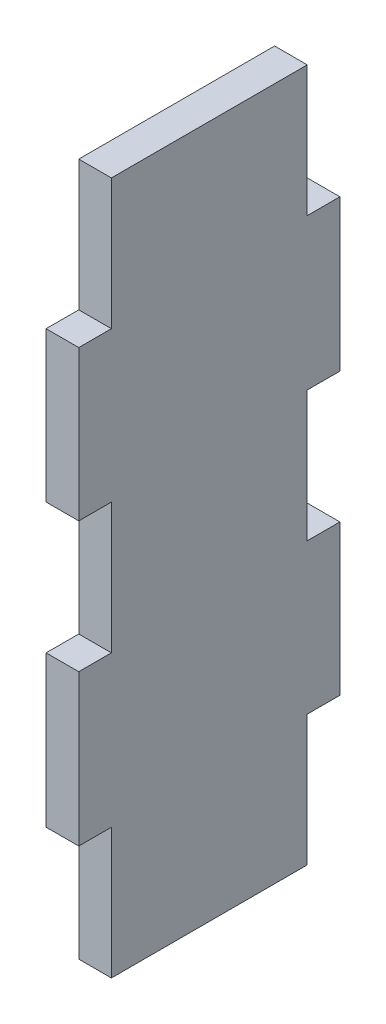
SolidWorks part; units mm, degrees
ref_plane "Front Plane" through (0, 0, 0) normal (0, 0, 1) x (1, 0, 0)
ref_plane "Top Plane" through (0, 0, 0) normal (0, 1, 0) x (1, 0, 0)
ref_plane "Right Plane" through (0, 0, 0) normal (1, 0, 0) x (0, 0, -1)
sketch "Sketch1" plane through (0, 0, 0) normal (0, 0, 1) x (1, 0, 0)
  line L0 (451.1075, 187.1755) -> (451.1075, 119.7813)
  line L1 (451.1075, 119.7813) -> (454.2825, 119.7813)
  line L2 (454.2825, 119.7813) -> (454.2825, 187.1755)
  line L3 (454.2825, 187.1755) -> (451.1075, 187.1755)
  dimension "D1" = 3.175
extrude "Boss-Extrude1" add sketch "Sketch1" against normal up to surface (25.4 mm away) contours L2 L3 L0 L1
sketch "Sketch2" plane through (454.2825, 0, 0) normal (1, 0, 0) x (0, 0, -1)
  line L0 (3.175, 84.4459) -> (3.175, 234.4049) construction
  line L1 (0, 187.1755) -> (3.175, 187.1755)
  line L2 (0, 187.1755) -> (0, 174.4755)
  line L3 (0, 174.4755) -> (3.175, 174.4755)
  line L4 (3.175, 187.1755) -> (3.175, 174.4755)
  line L5 (22.225, 234.4049) -> (22.225, 84.4459) construction
  line L6 (22.225, 174.4755) -> (25.4, 174.4755)
  line L7 (22.225, 174.4755) -> (22.225, 187.1755)
  line L8 (22.225, 187.1755) -> (25.4, 187.1755)
  line L9 (25.4, 174.4755) -> (25.4, 187.1755)
  line L10 (0, 119.7813) -> (0, 187.1755) construction
  line L11 (25.4, 119.7813) -> (22.225, 119.7813)
  line L12 (25.4, 119.7813) -> (25.4, 132.4813)
  line L13 (25.4, 132.4813) -> (22.225, 132.4813)
  line L14 (22.225, 119.7813) -> (22.225, 132.4813)
  line L15 (0, 119.7813) -> (3.175, 119.7813)
  line L16 (0, 119.7813) -> (0, 132.4813)
  line L17 (0, 132.4813) -> (3.175, 132.4813)
  line L18 (3.175, 119.7813) -> (3.175, 132.4813)
  line L19 (0, 147.1705) -> (3.175, 147.1705)
  line L20 (0, 147.1705) -> (0, 159.8705)
  line L21 (0, 159.8705) -> (3.175, 159.8705)
  line L22 (3.175, 147.1705) -> (3.175, 159.8705)
  line L23 (25.4, 119.7813) -> (25.4, 187.1755) construction
  line L24 (22.225, 147.0863) -> (25.4, 147.0863)
  line L25 (22.225, 147.0863) -> (22.225, 159.7863)
  line L26 (22.225, 159.7863) -> (25.4, 159.7863)
  line L27 (25.4, 147.0863) -> (25.4, 159.7863)
  dimension "D1" = 12.7
  dimension "D2" = 12.7
  dimension "D3" = 12.7
  dimension "D4" = 12.7
  dimension "D5" = 12.7
  dimension "D6" = 12.7
  dimension "D7" = 14.605
  dimension "D8" = 14.605
extrude "Cut-Extrude1" cut sketch "Sketch2" against normal blind 3.175
